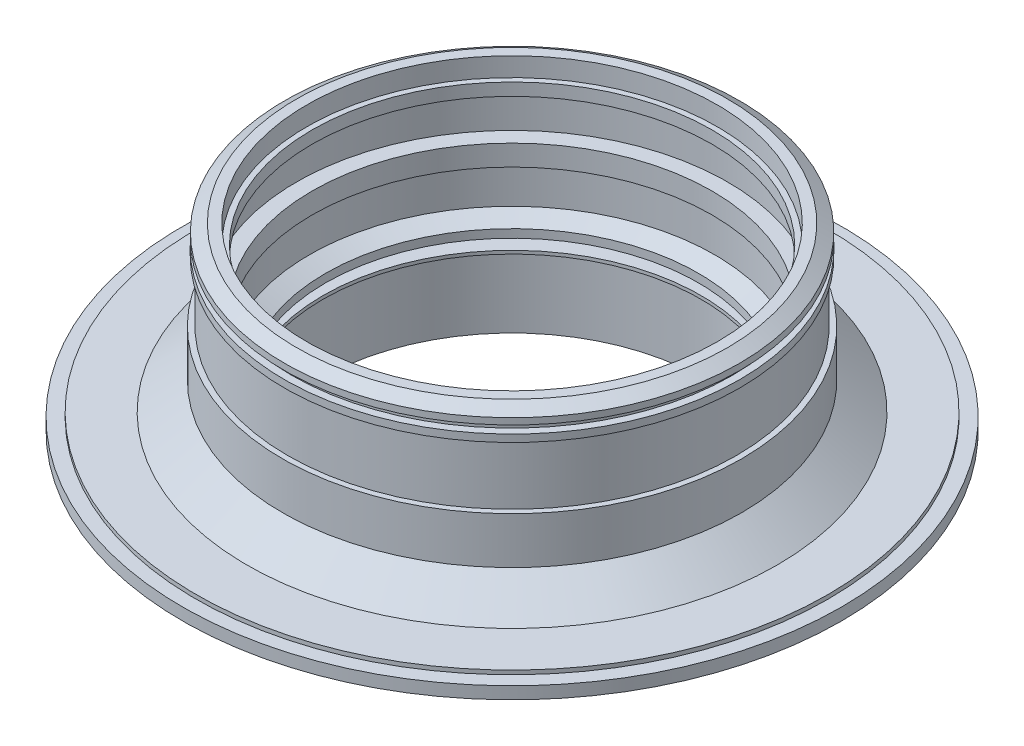
SolidWorks part; units mm, degrees
ref_plane "Front Plane" through (0, 0, 0) normal (0, 0, 1) x (1, 0, 0)
ref_plane "Top Plane" through (0, 0, 0) normal (0, 1, 0) x (1, 0, 0)
ref_plane "Right Plane" through (0, 0, 0) normal (1, 0, 0) x (0, 0, -1)
sketch "Sketch2" plane through (0, 0, 0) normal (0, 0, 1) x (1, 0, 0)
  line L0 (0, -27.768) -> (0, 1360.6325) construction
  line L1 (-117, 0) -> (-98.1423, 0)
  line L3 (-85, 10.2104) -> (-85, 27.5013)
  line L4 (-85, 27.5013) -> (-83, 27.5013)
  line L5 (-83, 27.5013) -> (-83, 49.7935)
  line L6 (-83, 49.7935) -> (-84.2566, 49.7935)
  line L7 (-84.2566, 49.7935) -> (-84.2566, 52.5)
  line L8 (-84.2566, 52.5) -> (-81.5426, 52.5)
  line L9 (-81.5426, 52.5) -> (-81.5426, 55.3639)
  line L10 (-81.5426, 55.3639) -> (-84.2109, 55.3639)
  line L11 (-84.2109, 55.3639) -> (-84.2109, 57.709)
  line L12 (-84.2109, 57.709) -> (-79.7682, 60.5)
  line L13 (-79.7682, 60.5) -> (-75.9793, 60.5)
  line L14 (-75.9793, 60.5) -> (-75.9793, 53.4793)
  line L15 (-75.9793, 53.4793) -> (-74, 53.4793)
  line L16 (-74, 53.4793) -> (-74, 48.8846)
  line L17 (-74, 26.2045) -> (-75, 26.2045)
  line L18 (-75, 26.2045) -> (-75, 12.9355)
  line L19 (-75, 12.9355) -> (-69, 10.0009)
  line L20 (-69, 10.0009) -> (-69, 6.9297)
  line L21 (-69, 6.9297) -> (-75.8188, 4.4478)
  line L22 (-75.8188, 4.4478) -> (-75.8188, 2.3447)
  line L23 (-75.8188, 2.3447) -> (-70, 2.3447)
  line L24 (-70, 2.3447) -> (-70, 1.1447)
  line L25 (-70, 1.1447) -> (-71, 1.1447)
  line L26 (-71, 1.1447) -> (-71, -24.8797)
  line L27 (-71, -24.8797) -> (-77.75, -24.8797)
  line L28 (-77.75, -24.8797) -> (-77.75, -17.3797)
  line L29 (-77.75, -17.3797) -> (-74.5, -17.3797)
  line L30 (-74.5, -17.3797) -> (-74.5, -2.65)
  line L31 (-74.5, -2.65) -> (-80.6472, -2.65)
  line L32 (-80.6472, -2.65) -> (-87.5, -9.2776)
  line L33 (-87.5, -9.2776) -> (-87.5, -12)
  line L34 (-87.5, -12) -> (-93.5, -12)
  line L35 (-93.5, -12) -> (-93.5, -6)
  line L36 (-93.5, -6) -> (-122, -6)
  line L37 (-122, -6) -> (-122, -1.5)
  line L38 (-122, -1.5) -> (-117, -1.5)
  line L39 (-117, -1.5) -> (-117, 0)
  line L40 (-85, 10.2104) -> (-98.1423, 0)
  line L41 (-74, 48.8846) -> (-79.7682, 48.8846)
  line L42 (-79.7682, 48.8846) -> (-79.7682, 33.8846)
  line L43 (-79.7682, 33.8846) -> (-74, 33.8846)
  line L44 (-74, 33.8846) -> (-74, 26.2045)
  dimension "D1" = 60.5
  dimension "D2" = 6
  dimension "D3" = 1.5
  dimension "D4" = 244
  dimension "D5" = 234
  dimension "D6" = 170
  dimension "D7" = 187
  dimension "D8" = 175
  dimension "D9" = 155.5
  dimension "D10" = 149
  dimension "D11" = 142
  dimension "D12" = 140
  dimension "D13" = 1.2
  dimension "D14" = 138
  dimension "D15" = 148
  dimension "D16" = 166
  dimension "D17" = 52.5
  dimension "D18" = 7.5
  dimension "D19" = 2.65
  dimension "D20" = 6
  dimension "D21" = 110
  dimension "D22" = 2.1031
  dimension "D23" = 150
  dimension "D24" = 142.156
  dimension "D25" = 10.2104
  dimension "D26" = 27.5013
  dimension "D27" = 2.714
  dimension "D28" = 49.7935
  dimension "D29" = 163.0853
  dimension "D30" = 2.3451
  dimension "D31" = 212.138
  dimension "D32" = 151.9586
  dimension "D33" = 7.0207
  dimension "D34" = 2.8639
  dimension "D35" = 84.2109
  dimension "D36" = 134.043
  dimension "D37" = 161.2945
  dimension "D38" = 18.8797
  dimension "D39" = 6.8188
  dimension "D40" = 3.7947
  dimension "D41" = 116.063
  dimension "D42" = 10.0009
  dimension "D43" = 26.2045
  dimension "D44" = 15
  dimension "D45" = 159.5364
  dimension "D46" = 33.8846
revolve "Revolve1" add sketch "Sketch2" angle 360 about L0
